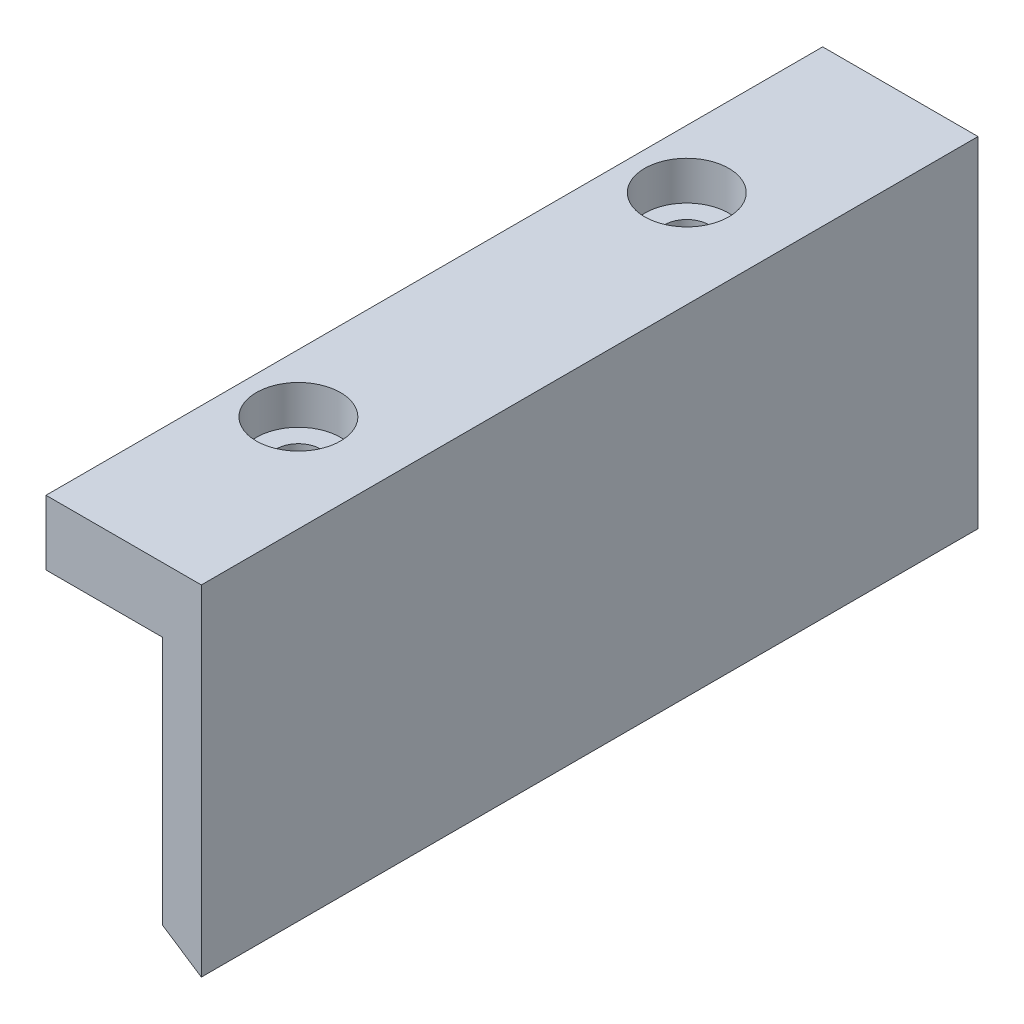
SolidWorks part; units mm, degrees
material "6061 Alloy"
ref_plane "Front Plane" through (0, 0, 0) normal (0, 0, 1) x (1, 0, 0)
ref_plane "Top Plane" through (0, 0, 0) normal (0, 1, 0) x (1, 0, 0)
ref_plane "Right Plane" through (0, 0, 0) normal (1, 0, 0) x (0, 0, -1)
sketch "Sketch2" plane through (0, 0, 0) normal (0, 0, 1) x (1, 0, 0)
  line L0 (85.25, 15) -> (85.25, 45.2)
  line L1 (70.25, 60.2) -> (0, 60.2)
  line L2 (0, 60.2) -> (0, 33.96)
  line L3 (0, 33.96) -> (-3, 35.94)
  line L4 (-3, 35.94) -> (-3, 24.26)
  line L5 (-3, 24.26) -> (0, 26.24)
  line L6 (0, 26.24) -> (0, 0)
  line L7 (0, 0) -> (70.25, 0)
  line L8 (30, 41.37) -> (30, 11.37)
  line L9 (40, 1.37) -> (70, 1.37)
  line L10 (80, 11.37) -> (80, 41.37)
  line L11 (70, 51.37) -> (40, 51.37)
  arc A0 (70.25, 0) -> (85.25, 15) centre (70.25, 15) ccw
  arc A1 (85.25, 45.2) -> (70.25, 60.2) centre (70.25, 45.2) ccw
  arc A2 (30, 11.37) -> (40, 1.37) centre (40, 11.37) ccw
  arc A3 (70, 1.37) -> (80, 11.37) centre (70, 11.37) ccw
  arc A4 (80, 41.37) -> (70, 51.37) centre (70, 41.37) ccw
  arc A5 (40, 51.37) -> (30, 41.37) centre (40, 41.37) ccw
  dimension "D3" = 15
  dimension "D7" = 10
  dimension "D1" = 85.25
  dimension "D2" = 60.2
  dimension "D4" = 3
  dimension "D5" = 11.68
  dimension "D6" = 7.72
  dimension "D8" = 50
  dimension "D9" = 50
  dimension "D10" = 5.25
  dimension "D11" = 1.37
sketch "Sketch3" plane through (0, 0, 0) normal (0, 0, 1) x (1, 0, 0)
  line L0 (0, 60.2) -> (0, 33.96) construction
  line L1 (0, 33.96) -> (-3, 35.94) construction
  line L2 (0, 60.2) -> (0, 33.96)
  line L3 (0, 33.96) -> (-3, 35.94)
  line L4 (0, 60.2) -> (-12, 60.2)
  line L5 (-12, 60.2) -> (-12, 55.2)
  line L6 (-12, 55.2) -> (-3, 55.2)
  line L7 (-3, 55.2) -> (-3, 35.94)
  dimension "D1" = 12
  dimension "D2" = 5
extrude "Boss-Extrude1" add sketch "Sketch3" along normal blind 60
hole_wizard "CBORE for M3 SHCS1" positions "Sketch4" profile "Sketch5" counterbore size "M3" standard "ANSI Metric"
sketch "Sketch4" plane through (0, 60.2, 0) normal (0, 1, 0) x (1, 0, 0)
  line L0 (-7.5, -15) -> (-7.5, -45) construction
  line L2 (0, 0) -> (-12, 0) construction
  line L3 (0, -60) -> (0, 0) construction
  line L4 (-12, -60) -> (-3, -60) construction
  point P0 (-7.5, -15)
  point P2 (-7.5, -45)
  point P16 (0, -30)
  point P17 (-7.5, -30)
  point P20 (-7.5, -60)
  dimension "D1" = 30
sketch "Sketch5" plane through (-7.5, 60.2, 15) normal (1, 0, 0) x (0, 0, 1)
  line L0 (0, 0) -> (0, 6.0215)
  line L1 (0, 6.0215) -> (1.7, 5)
  line L2 (1.7, 5) -> (1.7, 3)
  line L3 (1.7, 3) -> (3.25, 3)
  line L4 (3.25, 3) -> (3.25, 0)
  line L5 (3.25, 0) -> (0, 0)
  line L10 (0, 6.0215) -> (-1.7, 5) construction
  line L11 (0, -6.35) -> (0, 107.95) construction
  dimension "Hole Dia." = 3.4
  dimension "Hole Depth" = 5
  dimension "C'Bore Dia." = 6.5
  dimension "C'Bore Depth" = 3
  dimension "Drill Angle" = 118
